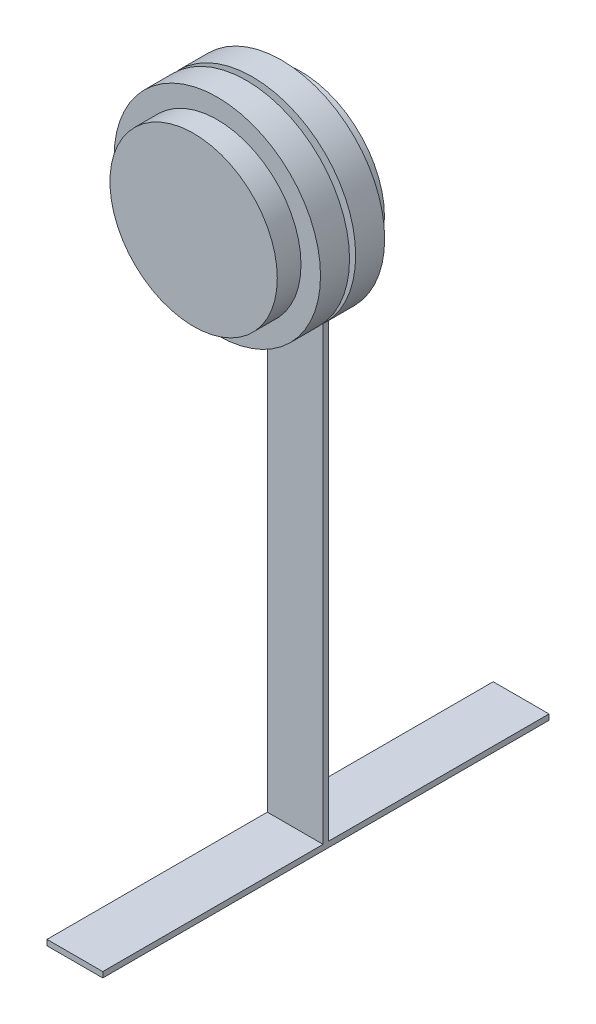
SolidWorks part; units mm, degrees
material "1023 Carbon Steel Sheet (SS)"
ref_plane "Front Plane" through (0, 0, 0) normal (0, 0, 1) x (1, 0, 0)
ref_plane "Top Plane" through (0, 0, 0) normal (0, 1, 0) x (1, 0, 0)
ref_plane "Right Plane" through (0, 0, 0) normal (1, 0, 0) x (0, 0, -1)
sketch "Sketch1" plane through (0, 0, 0) normal (0, 0, 1) x (1, 0, 0)
  circle A0 centre (0, 0) radius 38.1
  dimension "D1" = 76.2
extrude "Hub Center" add sketch "Sketch1" along normal blind 25.4 and the other way blind 23.4
sketch "Sketch2" plane through (0, 0, 0) normal (0, 0, 1) x (1, 0, 0)
  circle A0 centre (0, 0) radius 46.99
  dimension "D1" = 93.98
extrude "Inner Bearing" add sketch "Sketch2" along normal blind 13.208 from offset 1.397
sketch "Sketch3" plane through (0, 0, 0) normal (0, 0, 1) x (1, 0, 0)
  circle A0 centre (0, 0) radius 46.99
  circle A1 centre (0, 0) radius 46.99 construction
extrude "Outer Bearing" add sketch "Sketch3" against normal blind 13.208 from offset 1.397 offset against normal yes
sketch "Sketch4" plane through (0, 0, -23.4) normal (0, 0, -1) x (-1, 0, 0)
  line L0 (-12.7, -35.921) -> (-12.7, -261.62)
  line L1 (-12.7, -261.62) -> (12.7, -261.62)
  line L2 (12.7, -261.62) -> (12.7, -35.921)
  arc A0 (-12.7, -35.921) -> (12.7, -35.921) centre (0, 0) ccw
  circle A1 centre (0, 0) radius 38.1 construction
  point P6 (0, -38.1)
  dimension "D1" = 25.4
  dimension "D2" = 261.62
extrude "Tire Arm" add sketch "Sketch4" against normal blind 2.54
sketch "Sketch5" plane through (0, -261.62, 0) normal (0, -1, 0) x (1, 0, 0)
  line L0 (-12.7, -20.86) -> (12.7, -23.4) construction
  line L1 (12.7, -123.73) -> (-12.7, -123.73)
  line L2 (12.7, -123.73) -> (12.7, 79.47)
  line L3 (12.7, 79.47) -> (-12.7, 79.47)
  line L4 (-12.7, -123.73) -> (-12.7, 79.47)
  line L5 (12.7, -123.73) -> (-12.7, 79.47) construction
  line L6 (12.7, 79.47) -> (-12.7, -123.73) construction
  point P0 (0, -22.13)
  dimension "D1" = 203.2
  dimension "D2" = 25.4
extrude "Tire Contact Patch" add sketch "Sketch5" against normal blind 2.54
